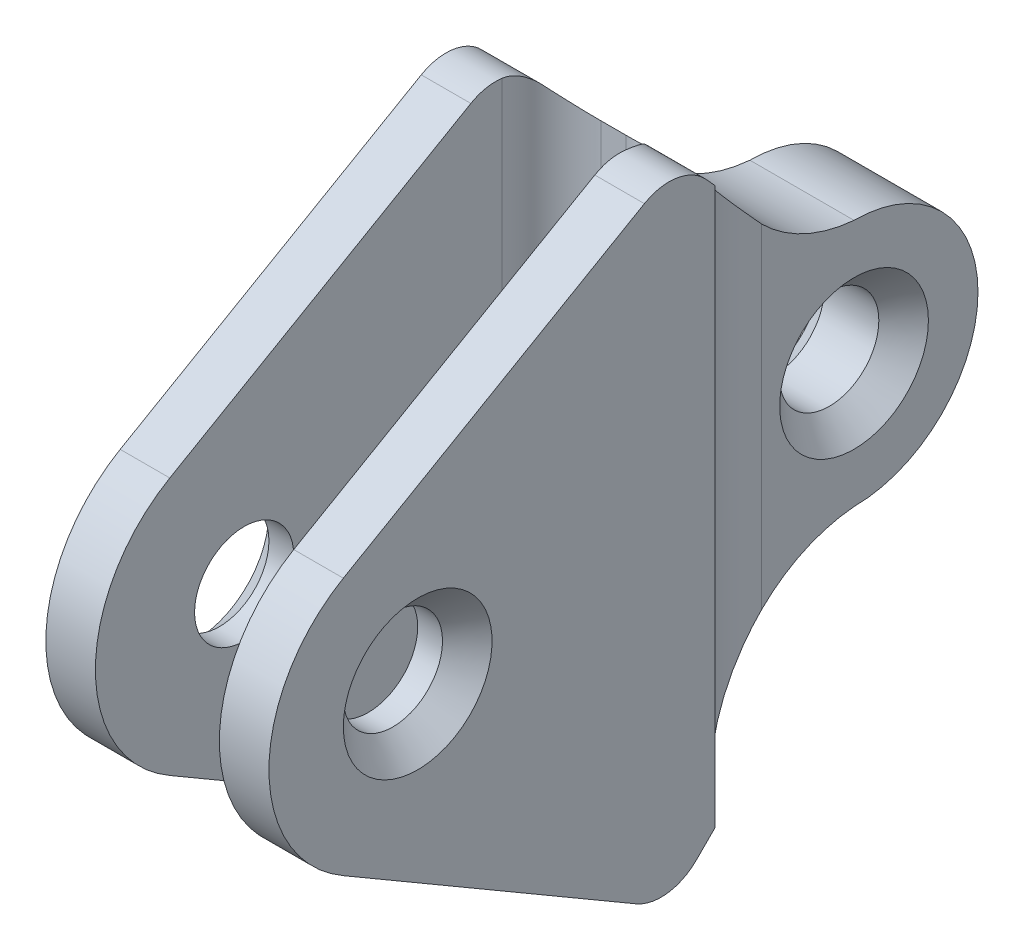
SolidWorks part; units mm, degrees
ref_plane "Front Plane" through (0, 0, 0) normal (0, 0, 1) x (1, 0, 0)
ref_plane "Top Plane" through (0, 0, 0) normal (0, 1, 0) x (1, 0, 0)
ref_plane "Right Plane" through (0, 0, 0) normal (1, 0, 0) x (0, 0, -1)
sketch "Sketch1" plane through (0, 0, 0) normal (0, 1, 0) x (1, 0, 0)
  line L0 (0, 0) -> (21, 0)
  line L1 (21, 0) -> (21, -43.6458)
  line L2 (0, 0) -> (0, -43.6458)
  line L3 (-12, -65) -> (-12, -155)
  line L4 (-12, -155) -> (-2, -155)
  line L5 (-2, -155) -> (-2, -100.4506)
  line L7 (23, -73) -> (23, -155)
  line L8 (23, -155) -> (33, -155)
  line L9 (33, -155) -> (33, -65)
  line L10 (8, -63) -> (13, -63)
  line L11 (-2, -100.4506) -> (-2, -73)
  line L12 (8, -63) -> (13, -63)
  arc A2 (-12, -65) -> (0, -43.6458) centre (-25, -43.6458) ccw
  arc A3 (21, -43.6458) -> (33, -65) centre (46, -43.6458) ccw
  arc A4 (-2, -73) -> (8, -63) centre (8, -73) cw
  arc A5 (13, -63) -> (23, -73) centre (13, -73) cw
  point P22 (23, -63)
  dimension "D7" = 25
  dimension "D8" = 25
  dimension "D11" = 10
  dimension "D12" = 10
  dimension "D1" = 12
  dimension "D2" = 12
  dimension "D3" = 25
  dimension "D4" = 45
  dimension "D5" = 65
  dimension "D6" = 65
  dimension "D9" = 92
  dimension "D10" = 155
  dimension "D13" = 155
extrude "Boss-Extrude1" add sketch "Sketch1" along normal blind 218 contours L10 A5 L7 L8 L9 A3 L1 L0 L2 A2 L3 L4 L5 L11 A4
sketch "Sketch3" plane through (0, 0, 0) normal (-1, 0, 0) x (0, 0, 1)
  line L0 (0, 218) -> (0, 0) construction
  line L1 (43.6458, 218) -> (43.6458, 0) construction
  line L2 (43.6458, 147.2394) -> (94.3182, 197.9117)
  line L3 (43.6458, 79.8859) -> (108.5648, 14.967)
  line L4 (25, 113.5627) -> (184.5037, 113.5627) construction
  line L5 (65, 168.5936) -> (65, 218)
  line L6 (65, 218) -> (65, 0) construction
  line L7 (65, 218) -> (0, 218)
  line L8 (0, 218) -> (0, 113.5627)
  line L9 (65, 58.5318) -> (65, 0)
  line L10 (65, 0) -> (0, 0)
  line L11 (0, 0) -> (0, 113.5627)
  circle A0 centre (25, 113.5627) radius 25
  circle A1 centre (25, 113.5627) radius 10
  arc A2 (25, 138.5627) -> (43.6458, 147.2394) centre (22.4326, 168.4526) ccw
  arc A3 (25, 88.5627) -> (43.6458, 79.8859) centre (22.4326, 58.6727) cw
  line M6 (0, 0) -> (43.6458, 0)
  line M7 (43.6458, 0) -> (43.6458, 218)
  line M8 (43.6458, 218) -> (0, 218)
  line M9 (0, 218) -> (0, 0)
  dimension "D2" = 50
  dimension "D3" = 20
  dimension "D4" = 30
  dimension "D5" = 30
  dimension "D1" = 25
  dimension "D6" = 45
  dimension "D7" = 45
extrude "Cut-Extrude1" cut sketch "Sketch3" against normal blind 218 contours A0 A2 M7 M8 M9 | A3 A0 M9 M6 M7
sketch "Sketch5" plane through (-12, 0, 0) normal (-1, 0, 0) x (0, 0, 1)
  line L0 (155, 218) -> (155, 0) construction
  line L1 (79.2827, 174.6136) -> (140, 139.5585)
  line L2 (43.6458, 147.2394) -> (43.6458, 218)
  line L3 (125, 113.5777) -> (115, 113.5777) construction
  line L4 (43.6458, 147.2394) -> (66.8992, 172.6975)
  line L5 (43.6458, 79.8859) -> (68.8242, 54.7076)
  line L6 (43.6458, 218) -> (155, 218)
  line L7 (80.8953, 53.1184) -> (140, 87.597)
  line L8 (155, 218) -> (155, 0)
  line L9 (155, 0) -> (43.6458, 0)
  line L10 (43.6458, 0) -> (43.6458, 79.8859)
  arc A0 (140, 87.597) -> (140, 139.5585) centre (125, 113.5777) ccw
  circle A1 centre (125, 113.5777) radius 10
  arc A2 (79.2827, 174.6136) -> (66.8992, 172.6975) centre (74.2827, 165.9534) ccw
  arc A3 (68.8242, 54.7076) -> (80.9728, 53.1636) centre (75.8953, 61.7786) ccw
  line M2 (65, 0) -> (155, 0)
  line M3 (155, 0) -> (155, 218)
  line M4 (155, 218) -> (65, 218)
  line M5 (65, 218) -> (65, 0)
  dimension "D2" = 60
  dimension "D3" = 20
  dimension "D4" = 20
  dimension "D6" = 20
  dimension "D1" = 30
  dimension "D5" = 30
extrude "Cut-Extrude2" cut sketch "Sketch5" against normal blind 218 contours A2 L1 A0 L8 L4 M4 M5 | L6 L2 L4 M5 | L10 L9 L5 M5 | A3 L5 A0 L7 M5 M2 M3
sketch "Sketch6" plane through (33, 0, 0) normal (1, 0, 0) x (0, 0, -1)
  circle A0 centre (-125, 113.5777) radius 10
  point P0 (-125, 113.5777)
  dimension "D1" = 20
extrude "Cut-Extrude3" cut sketch "Sketch6" against normal blind 218
sketch "Sketch7" plane through (21, 0, 0) normal (1, 0, 0) x (0, 0, -1)
  circle A0 centre (-25, 113.5627) radius 10
  point P0 (-25, 113.5627)
  dimension "D1" = 20
extrude "Cut-Extrude4" cut sketch "Sketch7" against normal blind 218
chamfer "Chamfer1" distance 5 angle 45 4 edges at (33, 113.5777, 115) (21, 113.5627, 15) (0, 113.5627, 15) (-12, 113.5777, 115)
